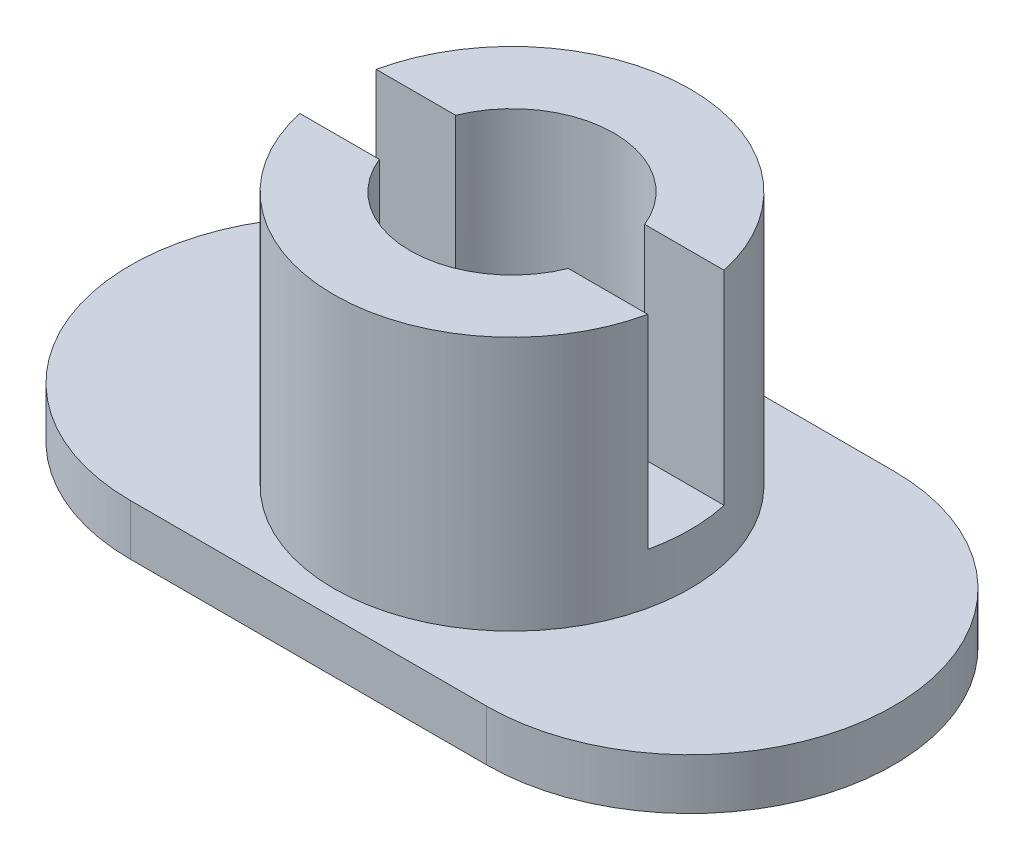
SolidWorks part; units mm, degrees
material "ABS"
ref_plane "Front Plane" through (0, 0, 0) normal (0, 0, 1) x (1, 0, 0)
ref_plane "Top Plane" through (0, 0, 0) normal (0, 1, 0) x (1, 0, 0)
ref_plane "Right Plane" through (0, 0, 0) normal (1, 0, 0) x (0, 0, -1)
sketch "Sketch1" plane through (0, 0, 0) normal (0, 1, 0) x (1, 0, 0)
  line L0 (-3.5, 0) -> (3.5, 0) construction
  line L1 (-3.5, 4) -> (3.5, 4)
  line L2 (-3.5, -4) -> (3.5, -4)
  arc A0 (-3.5, 4) -> (-3.5, -4) centre (-3.5, 0) ccw
  arc A1 (3.5, -4) -> (3.5, 4) centre (3.5, 0) ccw
  point P2 (0, 0)
  dimension "D1" = 8
  dimension "D2" = 15
extrude "Boss-Extrude1" add sketch "Sketch1" along normal blind 1
sketch "Sketch2" plane through (0, 1, 0) normal (0, 1, 0) x (1, 0, 0)
  circle A0 centre (0, 0) radius 3.5
  dimension "D1" = 7
extrude "Boss-Extrude2" add sketch "Sketch2" along normal blind 5
sketch "Sketch3" plane through (0, 6, 0) normal (0, 1, 0) x (1, 0, 0)
  circle A0 centre (0, 0) radius 2.0025
  dimension "D1" = 4.005
extrude "Cut-Extrude1" cut sketch "Sketch3" against normal through all
sketch "Sketch4" plane through (0, 6, 0) normal (0, 1, 0) x (1, 0, 0)
  line L0 (3.5, 0) -> (-3.5, 0) construction
  line L1 (-3.4187, 0.75) -> (3.4187, 0.75)
  line L2 (-3.4187, -0.75) -> (3.4187, -0.75)
  circle A0 centre (0, 0) radius 3.5 construction
  circle A1 centre (0, 0) radius 3.5 construction
  circle A2 centre (0, 0) radius 3.5
  circle M4 centre (0, 0) radius 2.0025
  circle M5 centre (0, 0) radius 3.5
  dimension "D1" = 0.75
extrude "Cut-Extrude2" cut sketch "Sketch4" against normal blind 4 contours L0 L2 M5 M4 | L0 A2 L1 M4 | L0 L1 M4 M5 | L0 A2 L2 M4
